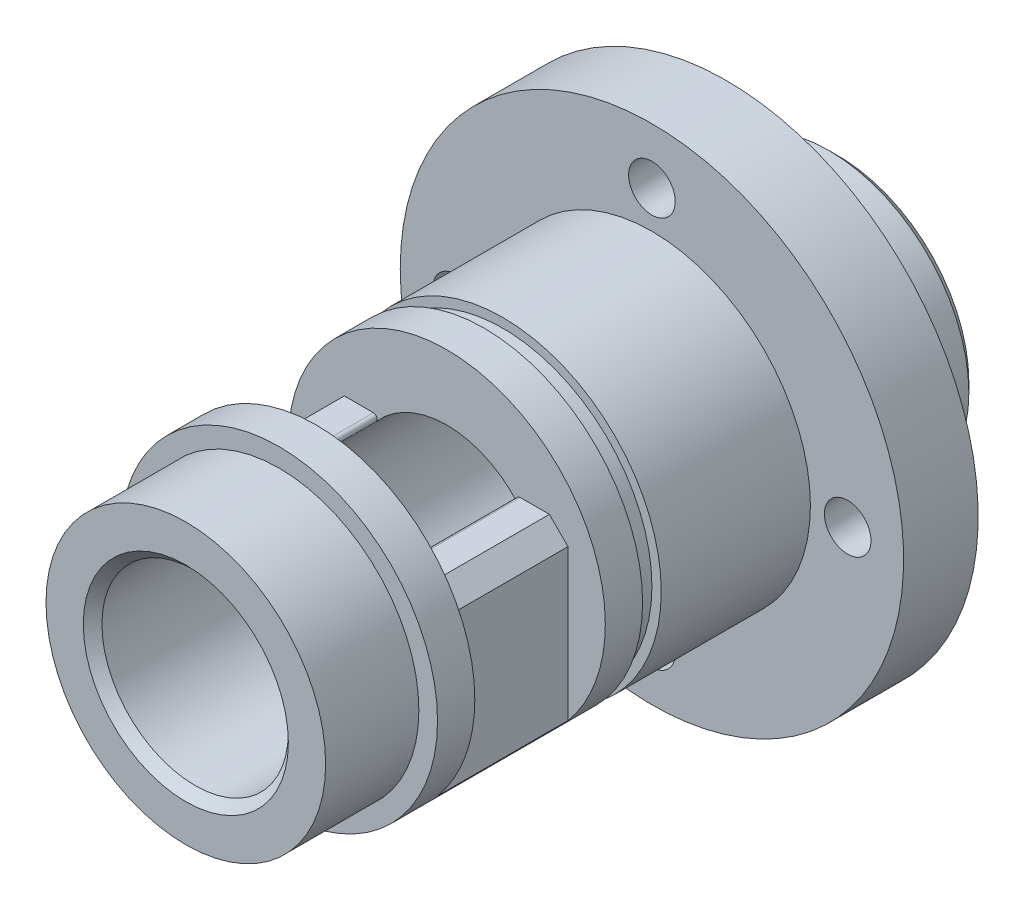
SolidWorks part; units mm, degrees
material "6061-O (SS)"
ref_plane "前视基准面" through (0, 0, 0) normal (0, 0, 1) x (1, 0, 0)
ref_plane "上视基准面" through (0, 0, 0) normal (0, 1, 0) x (1, 0, 0)
ref_plane "右视基准面" through (0, 0, 0) normal (1, 0, 0) x (0, 0, -1)
sketch "草图1" plane through (0, 0, 0) normal (0, 0, 1) x (1, 0, 0)
  circle A0 centre (0, 0) radius 8.5
  dimension "D1" = 17
extrude "凸台-拉伸1" add sketch "草图1" along normal blind 20
sketch "草图2" plane through (0, 0, 20) normal (0, 0, 1) x (1, 0, 0)
  circle A0 centre (0, 0) radius 7.5
  dimension "D1" = 15
extrude "凸台-拉伸2" add sketch "草图2" along normal blind 5
ref_plane "基准面1" through (0, 0, 8) normal (0, 0, 1) x (1, 0, 0)
sketch "草图3" plane through (0, 0, 8) normal (0, 0, 1) x (1, 0, 0)
  circle A0 centre (0, 0) radius 8.5 construction
  circle A1 centre (0, 0) radius 8.5
  circle A2 centre (0, 0) radius 8
  dimension "D1" = 0.5
extrude "切除-拉伸1" cut sketch "草图3" along normal blind 1
sketch "草图5" plane through (0, 0, 0) normal (0, 0, -1) x (-1, 0, 0)
  circle A0 centre (0, 0) radius 13.5
  dimension "D1" = 27
extrude "凸台-拉伸3" add sketch "草图5" along normal blind 4
sketch "草图7" plane through (0, 0, -4) normal (0, 0, -1) x (-1, 0, 0)
  circle A0 centre (0, 0) radius 7.5
  circle A1 centre (0, 0) radius 4 construction
  dimension "D1" = 15
  dimension "D2" = 8
extrude "凸台-拉伸4" add sketch "草图7" along normal blind 6
sketch "草图9" plane through (0, 0, -10) normal (0, 0, -1) x (-1, 0, 0)
  circle A0 centre (0, 0) radius 5
  dimension "D1" = 10
extrude "切除-拉伸3" cut sketch "草图9" against normal through all
chamfer "倒角2" distance 0.5 angle 45 1 edges at (-7.5, 0, -10)
ref_plane "基准面2" through (0, 0, 18) normal (0, 0, 1) x (1, 0, 0)
sketch "草图10" plane through (0, 0, 18) normal (0, 0, 1) x (1, 0, 0)
  line L0 (-7.7, 3.6) -> (7.7, 3.6)
  line L1 (-6.0208, -6) -> (6.0208, -6)
  circle A0 centre (0, 0) radius 8.5 construction
  arc A1 (-6.0208, -6) -> (6.0208, -6) centre (0, 0) ccw
  arc A2 (7.7, 3.6) -> (-7.7, 3.6) centre (0, 0) ccw
  dimension "D1" = 3.6
  dimension "D2" = 6
extrude "切除-拉伸4" cut sketch "草图10" against normal blind 7
sketch "草图12" plane through (0, 3.6, 0) normal (0, 1, 0) x (1, 0, 0)
  line L0 (0, 0) -> (0, -30.1443) construction
  line L1 (-7.7, -11) -> (-3.4699, -11) construction
  line L2 (-6.5, -11) -> (-10.5, -11)
  line L3 (-6.5, -11) -> (-6.5, -18)
  line L4 (-6.5, -18) -> (-10.5, -18)
  line L5 (-10.5, -11) -> (-10.5, -18)
  line L6 (-7.7, -18) -> (-3.4699, -18) construction
  line L7 (10.5, -11) -> (10.5, -18)
  line L8 (6.5, -18) -> (10.5, -18)
  line L9 (6.5, -11) -> (6.5, -18)
  line L10 (6.5, -11) -> (10.5, -11)
  dimension "D1" = 6.5
  dimension "D2" = 4
extrude "切除-拉伸5" cut sketch "草图12" against normal through all
chamfer "倒角3" distance 0.5 angle 45 1 edges at (-5, 0, 25)
chamfer "倒角4" distance 1 angle 45 2 edges at (6.5, 3.6, 14.5) (-6.5, 3.6, 14.5)
fillet "圆角1" radius 0.2 2 edges at (-3.4699, 3.6, 14.5) (3.4699, 3.6, 14.5)
sketch "草图13" plane through (0, 0, -4) normal (0, 0, -1) x (-1, 0, 0)
  circle A0 centre (0, 0) radius 10.5 construction
  point P3 (10.5, 0)
  point P7 (0, -10.5)
  point P8 (-10.5, 0)
  point P9 (0, 10.5)
  point P10 (0, 0)
  dimension "D1" = 21
  dimension "D2" = 4
hole_wizard "M3 螺纹孔1" positions "草图14" profile "草图15" tap size "M3" standard "GB" end condition up to next
sketch "草图14" plane through (0, 0, -4) normal (0, 0, -1) x (-1, 0, 0)
  point P0 (-10.5, 0)
  point P3 (0, 10.5)
  point P6 (10.5, 0)
  point P9 (0, -10.5)
sketch "草图15" plane through (10.5, 0, -4) normal (1, 0, 0) x (0, 1, 0)
  line L0 (0, 0) -> (0, 4)
  line L1 (0, 4) -> (1.25, 4)
  line L2 (1.25, 4) -> (1.25, 0)
  line L5 (1.25, 0) -> (0, 0)
  line L11 (0, -6.35) -> (0, 107.95) construction
  dimension "通孔螺纹孔钻头直径" = 2.5
  dimension "通孔螺纹孔钻头深度" = 4
cosmetic thread "孔螺蚊线1" parameters "D2"=3
cosmetic thread "孔螺蚊线2" parameters "D2"=3
cosmetic thread "孔螺蚊线3" parameters "D2"=3
cosmetic thread "孔螺蚊线4" parameters "D2"=3
